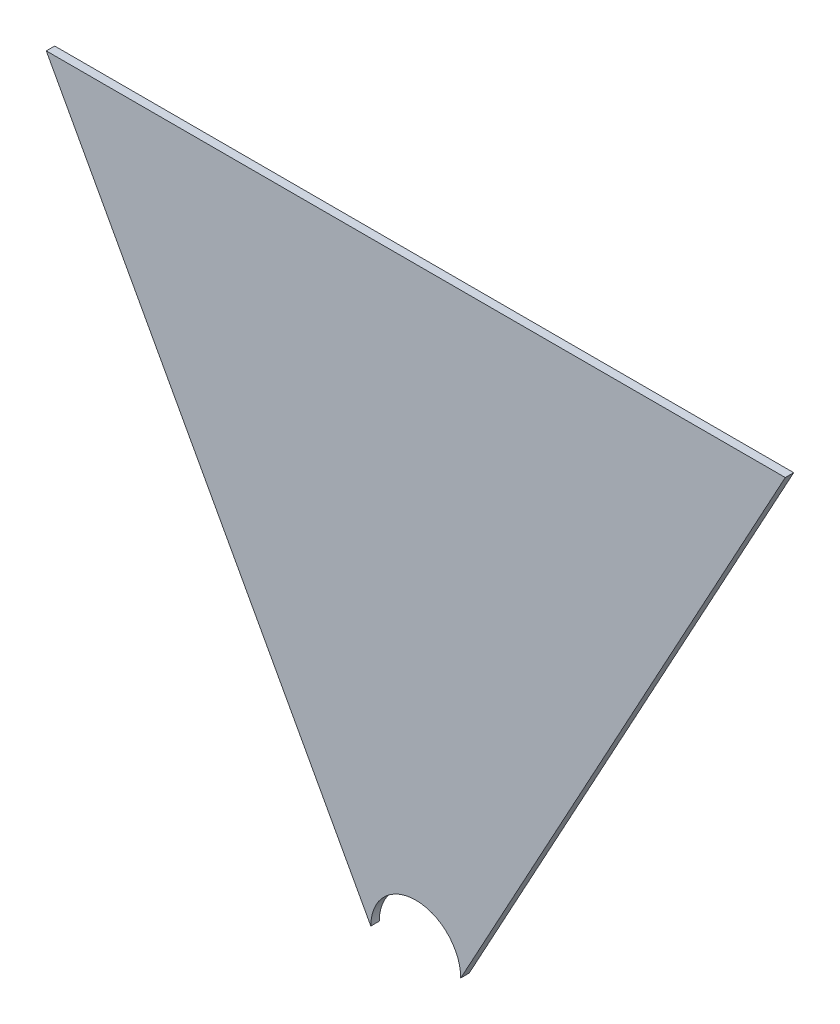
SolidWorks part; units mm, degrees
ref_plane "Alzado" through (0, 0, 0) normal (0, 0, 1) x (1, 0, 0)
ref_plane "Planta" through (0, 0, 0) normal (0, 1, 0) x (1, 0, 0)
ref_plane "Vista lateral" through (0, 0, 0) normal (1, 0, 0) x (0, 0, -1)
sketch "Croquis1" plane through (0, 0, 0) normal (0, 0, 1) x (1, 0, 0)
  line L0 (-131.5, 212) -> (131.5, 212)
  line L1 (16, 0) -> (131.5, 212)
  line L2 (-16, 0) -> (-131.5, 212)
  arc A0 (16, 0) -> (-16, 0) centre (0, 0) ccw
  dimension "D1" = 16
  dimension "D2" = 212
  dimension "D3" = 263
  dimension "D4" = 131.5
extrude "Saliente-Extruir1" add sketch "Croquis1" along normal blind 3
